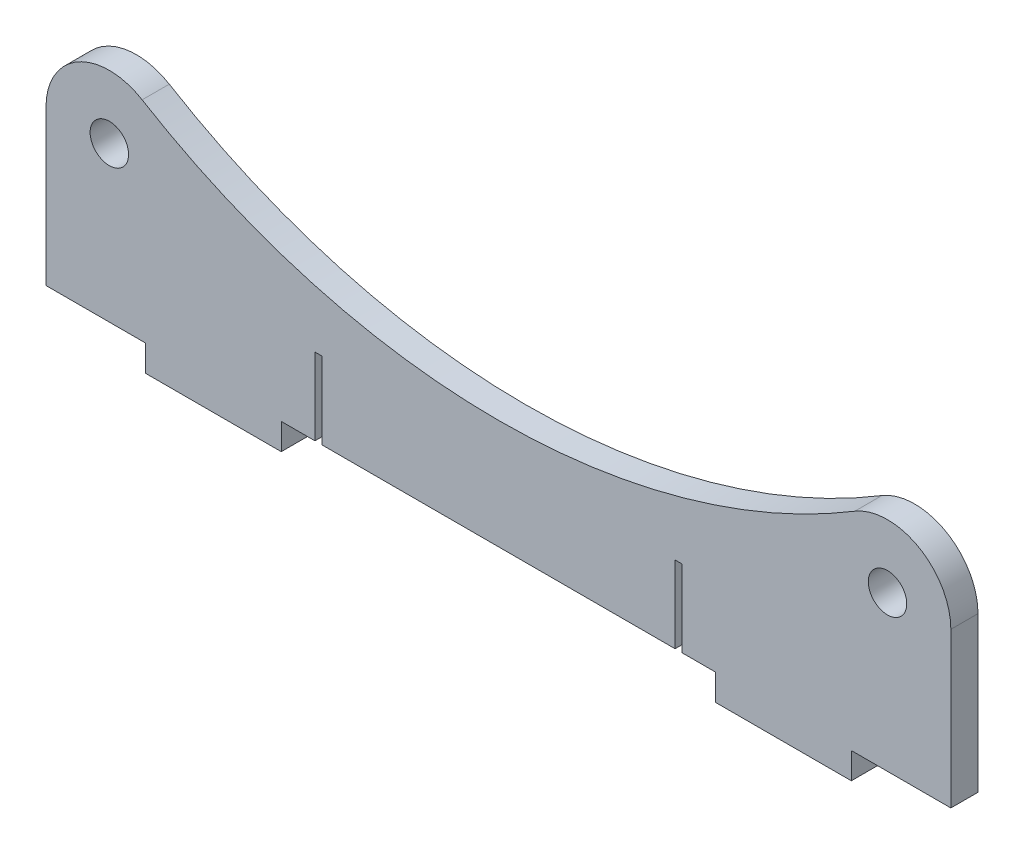
SolidWorks part; units mm, degrees
ref_plane "Plano frontal" through (0, 0, 0) normal (0, 0, 1) x (1, 0, 0)
ref_plane "Plano superior" through (0, 0, 0) normal (0, 1, 0) x (1, 0, 0)
ref_plane "Plano direito" through (0, 0, 0) normal (1, 0, 0) x (0, 0, -1)
sketch "Esboço1" plane through (0, 0, 0) normal (0, 0, 1) x (1, 0, 0)
  line L0 (-100, 30) -> (-100, -10)
  line L1 (-100, -10) -> (100, -10)
  line L2 (100, -10) -> (100, 30)
  line L3 (-78, -10) -> (-78, -4.2)
  line L4 (-78, -4.2) -> (-48, -4.2)
  line L5 (-48, -4.2) -> (-48, -10)
  line L6 (0, -10) -> (0, 20) construction
  line L7 (48, -4.2) -> (48, -10)
  line L8 (78, -4.2) -> (48, -4.2)
  line L9 (78, -10) -> (78, -4.2)
  line L10 (-100, -4.2) -> (100, -4.2)
  circle A0 centre (0, 99.6951) radius 99.6951
  circle A1 centre (-86, 30) radius 11 construction
  circle A2 centre (86, 30) radius 11 construction
  circle A3 centre (-86, 30) radius 14
  circle A4 centre (86, 30) radius 14
  arc A5 (-78.7506, 41.9769) -> (78.7506, 41.9769) centre (0, 172.0833) ccw
  circle A6 centre (-86, 30) radius 4.25
  circle A7 centre (86, 30) radius 4.25
  dimension "D2" = 22
  dimension "D3" = 30
  dimension "D4" = 3
  dimension "D7" = 30
  dimension "D11" = 8.5
  dimension "D12" = 172
  dimension "D6" = 40
  dimension "D8" = 5.8
  dimension "D9" = 22
  dimension "D10" = 30
  dimension "D5" = 3
extrude "Ressalto-extrusão1" add sketch "Esboço1" along normal blind 6 contours A4 A0 A3 L0 L10 L4 L8 L2 | A0 A3 A6 | A0 A3 | A4 A0 A7 | A0 A4 | A5 A3 A0 A4 | L5 L4 L3 L1 | L1 L9 L8 L7
sketch "Esboço2" plane through (0, 0, 6) normal (0, 0, 1) x (1, 0, 0)
  line L0 (-41.55, -7.2) -> (-38.05, -7.2) construction
  line L1 (-41.55, -4.2) -> (-41.55, -10.2) construction
  line L2 (-38.05, -10.2) -> (-38.05, -4.2) construction
  line L3 (-39.8, -7.2) -> (-39.8, 12.8) construction
  line L4 (-39.05, -7.2) -> (-39.05, 12.8)
  line L5 (-40.55, -7.2) -> (-40.55, 12.8)
  line L6 (-40.55, 12.8) -> (-39.05, 12.8)
  line L7 (-40.55, -7.2) -> (-39.05, -7.2)
  line L8 (0, 20) -> (0, -4.2) construction
  line L9 (4.3, -4.2) -> (-58.4833, -4.2) construction
  line L10 (39.8, -7.2) -> (39.8, 12.8) construction
  line L11 (41.55, -7.2) -> (38.05, -7.2) construction
  line L12 (40.55, -7.2) -> (39.05, -7.2)
  line L13 (40.55, 12.8) -> (39.05, 12.8)
  line L14 (40.55, -7.2) -> (40.55, 12.8)
  line L15 (39.05, -7.2) -> (39.05, 12.8)
  arc A0 (-78.7506, 41.9769) -> (78.7506, 41.9769) centre (0, 172.0833) ccw construction
  dimension "D1" = 20
  dimension "D2" = 0.75
  dimension "D3" = 0.75
extrude "Corte-extrusão1" cut sketch "Esboço2" against normal blind 25.5
